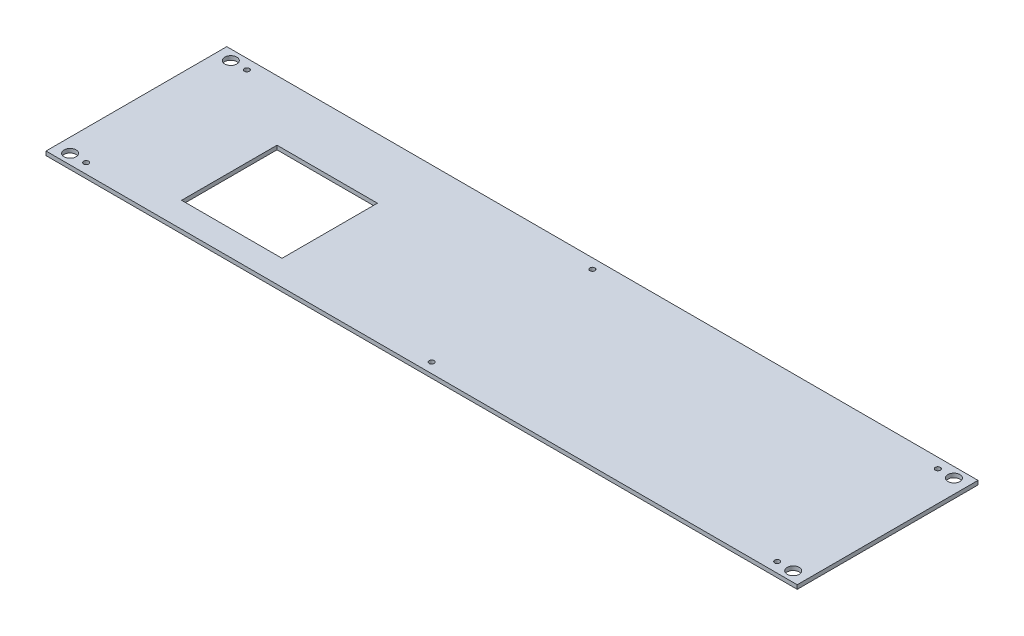
SolidWorks part; units mm, degrees
ref_plane "Front Plane" through (0, 0, 0) normal (0, 0, 1) x (1, 0, 0)
ref_plane "Top Plane" through (0, 0, 0) normal (0, 1, 0) x (1, 0, 0)
ref_plane "Right Plane" through (0, 0, 0) normal (1, 0, 0) x (0, 0, -1)
sketch "Sketch1" plane through (0, 0, 0) normal (0, 1, 0) x (1, 0, 0)
  line L0 (0, 90) -> (0, -90) construction
  line L1 (-374, -90) -> (374, -90)
  line L2 (-374, -90) -> (-374, 90)
  line L3 (-374, 90) -> (374, 90)
  line L4 (374, -90) -> (374, 90)
  line L5 (-374, -90) -> (374, 90) construction
  line L6 (-374, 90) -> (374, -90) construction
  line L7 (-374, 0) -> (374, 0) construction
  line L9 (-264, -65) -> (-164, -65)
  line L10 (-264, -65) -> (-264, 30)
  line L11 (-264, 30) -> (-164, 30)
  line L12 (-164, -65) -> (-164, 30)
  line L13 (-264, -65) -> (-164, 30) construction
  line L14 (-264, 30) -> (-164, -65) construction
  circle A0 centre (-344, 80) radius 2.5
  circle A1 centre (0, 80) radius 2.5
  circle A2 centre (344, 80) radius 2.5
  circle A3 centre (-344, -80) radius 2.5
  circle A4 centre (0, -80) radius 2.5
  circle A5 centre (344, -80) radius 2.5
  circle A6 centre (-360, 80) radius 6
  circle A7 centre (-360, -80) radius 6
  circle A8 centre (360, -80) radius 6
  circle A9 centre (360, 80) radius 6
  point P0 (0, 0)
  point P26 (-214, -17.5)
  dimension "D3" = 5
  dimension "D4" = 5
  dimension "D7" = 30
  dimension "D8" = 12
  dimension "D1" = 180
  dimension "D2" = 748
  dimension "D5" = 10
  dimension "D6" = 10
  dimension "D9" = 10
  dimension "D10" = 14
  dimension "D11" = 110
  dimension "D12" = 60
  dimension "D13" = 25
  dimension "D14" = 100
extrude "Boss-Extrude1" add sketch "Sketch1" along normal blind 4
